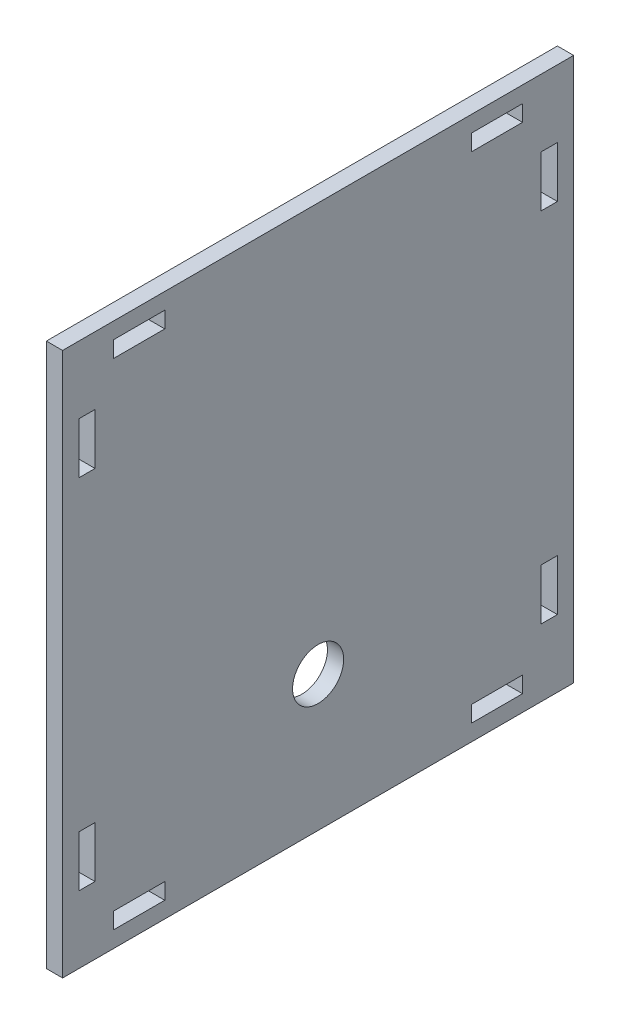
SolidWorks part; units mm, degrees
ref_plane "Front Plane" through (0, 0, 0) normal (0, 0, 1) x (1, 0, 0)
ref_plane "Top Plane" through (0, 0, 0) normal (0, 1, 0) x (1, 0, 0)
ref_plane "Right Plane" through (0, 0, 0) normal (1, 0, 0) x (0, 0, -1)
sketch "Sketch1" plane through (0, 0, 0) normal (1, 0, 0) x (0, 0, -1)
  line L0 (50, 106.35) -> (50, 41.5962) construction
  line L1 (0, 0) -> (100, 0)
  line L2 (0, 0) -> (0, 106.35)
  line L3 (0, 106.35) -> (100, 106.35)
  line L4 (100, 0) -> (100, 106.35)
  line L5 (3.175, 83.175) -> (6.35, 83.175)
  line L6 (3.175, 83.175) -> (3.175, 93.175)
  line L7 (3.175, 93.175) -> (6.35, 93.175)
  line L8 (6.35, 83.175) -> (6.35, 93.175)
  line L9 (10, 103.175) -> (20, 103.175)
  line L10 (10, 103.175) -> (10, 100)
  line L11 (10, 100) -> (20, 100)
  line L12 (20, 103.175) -> (20, 100)
  line L13 (80, 103.175) -> (80, 100)
  line L14 (90, 100) -> (80, 100)
  line L15 (90, 103.175) -> (90, 100)
  line L16 (90, 103.175) -> (80, 103.175)
  line L17 (93.65, 83.175) -> (93.65, 93.175)
  line L18 (96.825, 93.175) -> (93.65, 93.175)
  line L19 (96.825, 83.175) -> (96.825, 93.175)
  line L20 (96.825, 83.175) -> (93.65, 83.175)
  line L21 (0, 53.175) -> (72.9598, 53.175) construction
  line L22 (96.825, 23.175) -> (93.65, 23.175)
  line L23 (96.825, 23.175) -> (96.825, 13.175)
  line L24 (96.825, 13.175) -> (93.65, 13.175)
  line L25 (93.65, 23.175) -> (93.65, 13.175)
  line L26 (90, 3.175) -> (80, 3.175)
  line L27 (90, 3.175) -> (90, 6.35)
  line L28 (90, 6.35) -> (80, 6.35)
  line L29 (80, 3.175) -> (80, 6.35)
  line L30 (20, 3.175) -> (20, 6.35)
  line L31 (10, 6.35) -> (20, 6.35)
  line L32 (10, 3.175) -> (10, 6.35)
  line L33 (10, 3.175) -> (20, 3.175)
  line L34 (6.35, 23.175) -> (6.35, 13.175)
  line L35 (3.175, 13.175) -> (6.35, 13.175)
  line L36 (3.175, 23.175) -> (3.175, 13.175)
  line L37 (3.175, 23.175) -> (6.35, 23.175)
  circle A0 centre (50, 26.5093) radius 5
  dimension "D9" = 3.175
  dimension "D1" = 100
  dimension "D2" = 106.35
  dimension "D3" = 3.175
  dimension "D4" = 13.175
  dimension "D5" = 3.175
  dimension "D6" = 10
  dimension "D7" = 10
  dimension "D8" = 3.175
  dimension "D10" = 10
extrude "Boss-Extrude1" add sketch "Sketch1" along normal blind 3.175
